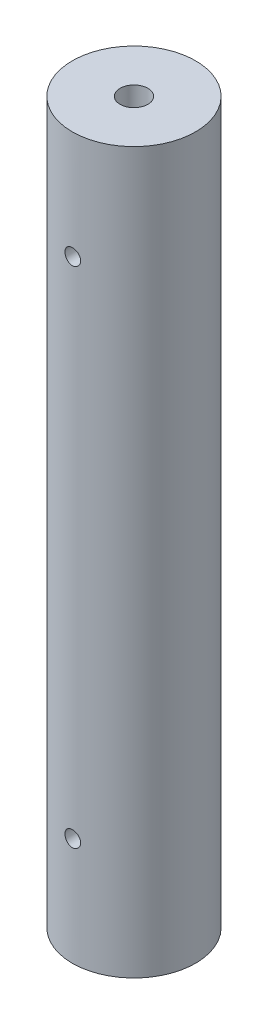
SolidWorks part; units mm, degrees
ref_plane "Front" through (0, 0, 0) normal (0, 0, 1) x (1, 0, 0)
ref_plane "Top" through (0, 0, 0) normal (0, 1, 0) x (1, 0, 0)
ref_plane "Right" through (0, 0, 0) normal (1, 0, 0) x (0, 0, -1)
sketch "Sketch1" plane through (0, 0, 0) normal (0, 1, 0) x (1, 0, 0)
  circle A0 centre (0, 0) radius 5
extrude "Boss-Extrude1" add sketch "Sketch1" along normal blind 58.42
hole_wizard "#4-40 Tapped Hole1" positions "Sketch2" profile "Sketch4" tap size "#4-40" standard "ANSI Inch"
sketch "Sketch2" plane through (0, 58.42, 0) normal (0, 1, 0) x (1, 0, 0)
  point P0 (0, 0)
sketch "Sketch4" plane through (0, 58.42, 0) normal (1, 0, 0) x (0, 0, 1)
  line L0 (0, 0) -> (0, 10.2042)
  line L1 (0, 10.2042) -> (1.1303, 9.525)
  line L2 (1.1303, 9.525) -> (1.1303, 0)
  line L5 (1.1303, 0) -> (0, 0)
  line L10 (0, 10.2042) -> (-1.1303, 9.525) construction
  line L11 (0, -6.35) -> (0, 107.95) construction
  dimension "Tap Drill Dia." = 2.2606
  dimension "Tap Drill Depth" = 9.525
  dimension "Drill Angle" = 118
cosmetic thread "Hole Thread2" parameters "D1"=7.62, "D2"=2.8448
hole_wizard "#4-40 Tapped Hole2" positions "Sketch5" profile "Sketch6" tap size "#4-40" standard "ANSI Inch"
sketch "Sketch5" plane through (0, 0, 0) normal (0, -1, 0) x (-1, 0, 0)
  point P0 (0, 0)
sketch "Sketch6" plane through (0, 0, 0) normal (1, 0, 0) x (0, 0, -1)
  line L0 (0, 0) -> (0, 10.2042)
  line L1 (0, 10.2042) -> (1.1303, 9.525)
  line L2 (1.1303, 9.525) -> (1.1303, 0)
  line L5 (1.1303, 0) -> (0, 0)
  line L10 (0, 10.2042) -> (-1.1303, 9.525) construction
  line L11 (0, -6.35) -> (0, 107.95) construction
  dimension "Tap Drill Dia." = 2.2606
  dimension "Tap Drill Depth" = 9.525
  dimension "Drill Angle" = 118
sketch "Sketch7" plane through (0, 0, 0) normal (0, 0, 1) x (1, 0, 0)
  circle A0 centre (0, 49.657) radius 0.635
  circle A1 centre (0, 8.763) radius 0.635
extrude "Cut-Extrude1" cut sketch "Sketch7" against normal through all both and the other way through all
